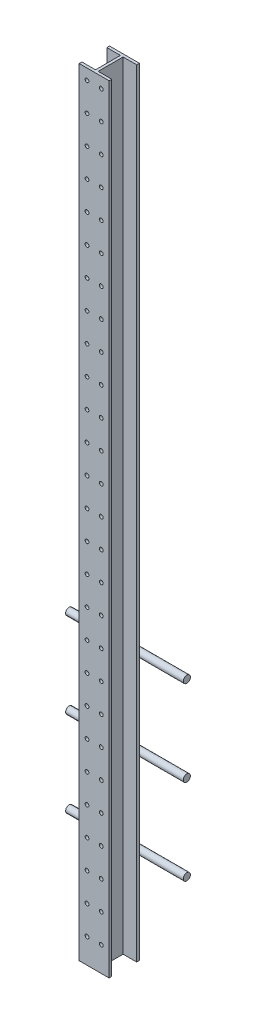
SolidWorks part; units mm, degrees
ref_plane "Front Plane" through (0, 0, 0) normal (0, 0, 1) x (1, 0, 0)
ref_plane "Top Plane" through (0, 0, 0) normal (0, 1, 0) x (1, 0, 0)
ref_plane "Right Plane" through (0, 0, 0) normal (1, 0, 0) x (0, 0, -1)
sketch "Sketch1" plane through (0, 0, 0) normal (0, 1, 0) x (1, 0, 0)
  line L0 (-4.7625, 9.525) -> (-4.7625, 98.425)
  line L1 (-4.7625, 98.425) -> (-53.213, 98.425)
  line L2 (-53.213, 98.425) -> (-53.213, 107.95)
  line L3 (-53.213, 107.95) -> (53.213, 107.95)
  line L4 (53.213, 107.95) -> (53.213, 98.425)
  line L5 (53.213, 98.425) -> (4.7625, 98.425)
  line L6 (4.7625, 98.425) -> (4.7625, 9.525)
  line L7 (4.7625, 9.525) -> (53.213, 9.525)
  line L8 (53.213, 9.525) -> (53.213, 0)
  line L9 (53.213, 0) -> (-53.213, 0)
  line L10 (-53.213, 0) -> (-53.213, 9.525)
  line L11 (-53.213, 9.525) -> (-4.7625, 9.525)
  line L12 (-4.7625, 9.525) -> (4.7625, 9.525) construction
  point P2 (0, 0)
  point P13 (0, 9.525)
  dimension "D1" = 106.426
  dimension "D2" = 9.525
  dimension "D3" = 9.525
  dimension "D4" = 107.95
  dimension "D5" = 9.525
extrude "Boss-Extrude1" add sketch "Sketch1" along normal blind 2768.6
hole_wizard "1/2 Clearance Hole1" positions "Sketch2" profile "Sketch3" hole size "1/2" standard "ANSI Inch" end condition up to next
sketch "Sketch2" plane through (0, 0, 0) normal (0, 0, 1) x (1, 0, 0)
  line L0 (-53.213, 0) -> (53.213, 0) construction
  line L1 (25.4, 88.9) -> (-25.4, 88.9) construction
  point P0 (25.4, 88.9)
  point P6 (-25.4, 88.9)
  point P14 (0, 88.9)
  dimension "D1" = 88.9
  dimension "D2" = 50.8
sketch "Sketch3" plane through (25.4, 88.9, 0) normal (1, 0, 0) x (0, -1, 0)
  line L0 (0, 0) -> (0, 9.525)
  line L1 (0, 9.525) -> (6.7462, 9.525)
  line L2 (6.7462, 9.525) -> (6.7462, 0)
  line L5 (6.7462, 0) -> (0, 0)
  line L11 (0, -6.35) -> (0, 107.95) construction
  dimension "Thru Hole Dia." = 13.4925
  dimension "Thru Hole Depth" = 9.525
pattern_linear "LPattern1" count 27 spacing 101.6 along (0, 1, 0) of "1/2 Clearance Hole1"
sketch "Sketch4" plane through (0, 0, 0) normal (1, 0, 0) x (0, 0, -1)
  line L2 (107.95, 330.2) -> (120.65, 330.2) construction
  line L3 (107.95, 2768.6) -> (107.95, 0) construction
  circle A0 centre (120.65, 330.2) radius 12.7
  dimension "D2" = 25.4
  dimension "D1" = 330.2
  dimension "D3" = 12.7
extrude "Boss-Extrude2" add sketch "Sketch4" along normal blind 209.55 and the other way blind 209.55 separate body
pattern_linear "LPattern2" count 3 spacing 304.8 along (0, 1, 0) of "Boss-Extrude2"
equation "\"D3@Sketch1\"=\"D2@Sketch1\""
equation "\"D5@Sketch1\"=\"D2@Sketch1\""
